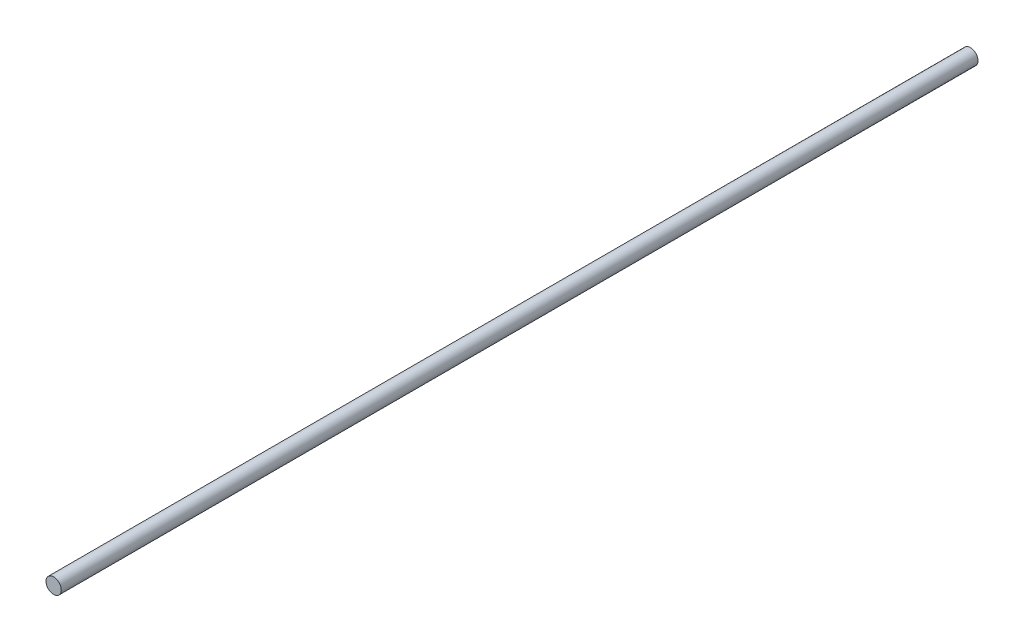
SolidWorks part; units mm, degrees
ref_plane "Front Plane" through (0, 0, 0) normal (0, 0, 1) x (1, 0, 0)
ref_plane "Top Plane" through (0, 0, 0) normal (0, 1, 0) x (1, 0, 0)
ref_plane "Right Plane" through (0, 0, 0) normal (1, 0, 0) x (0, 0, -1)
sketch "Sketch1" plane through (0, 0, 0) normal (0, 0, 1) x (1, 0, 0)
  circle A0 centre (0, 0) radius 3.9688
  dimension "D1" = 7.9375
extrude "Boss-Extrude1" add sketch "Sketch1" along normal blind 476.25
